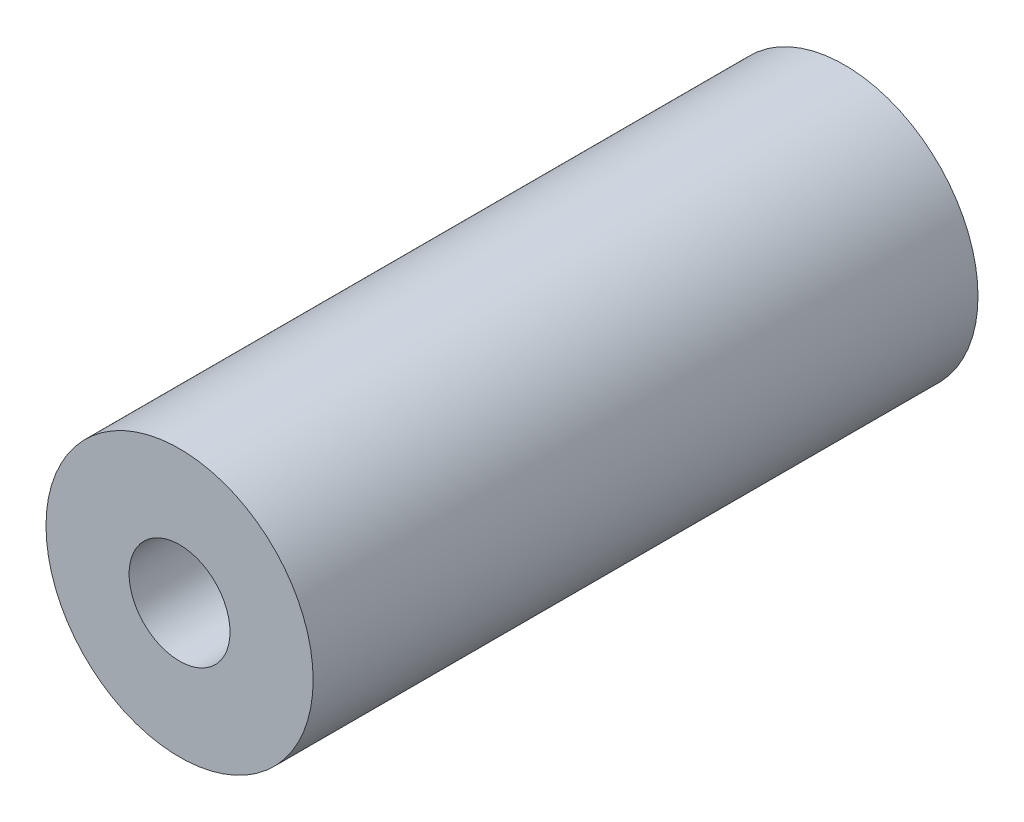
SolidWorks part; units mm, degrees
ref_plane "Front Plane" through (0, 0, 0) normal (0, 0, 1) x (1, 0, 0)
ref_plane "Top Plane" through (0, 0, 0) normal (0, 1, 0) x (1, 0, 0)
ref_plane "Right Plane" through (0, 0, 0) normal (1, 0, 0) x (0, 0, -1)
sketch "Sketch1" plane through (0, 0, 0) normal (0, 0, 1) x (1, 0, 0)
  circle A0 centre (0, 0) radius 30.6172
  circle A1 centre (0, 0) radius 11.5672
  dimension "D1" = 61.2343
  dimension "D2" = 23.1343
extrude "Boss-Extrude1" add sketch "Sketch1" along normal blind 152.4
